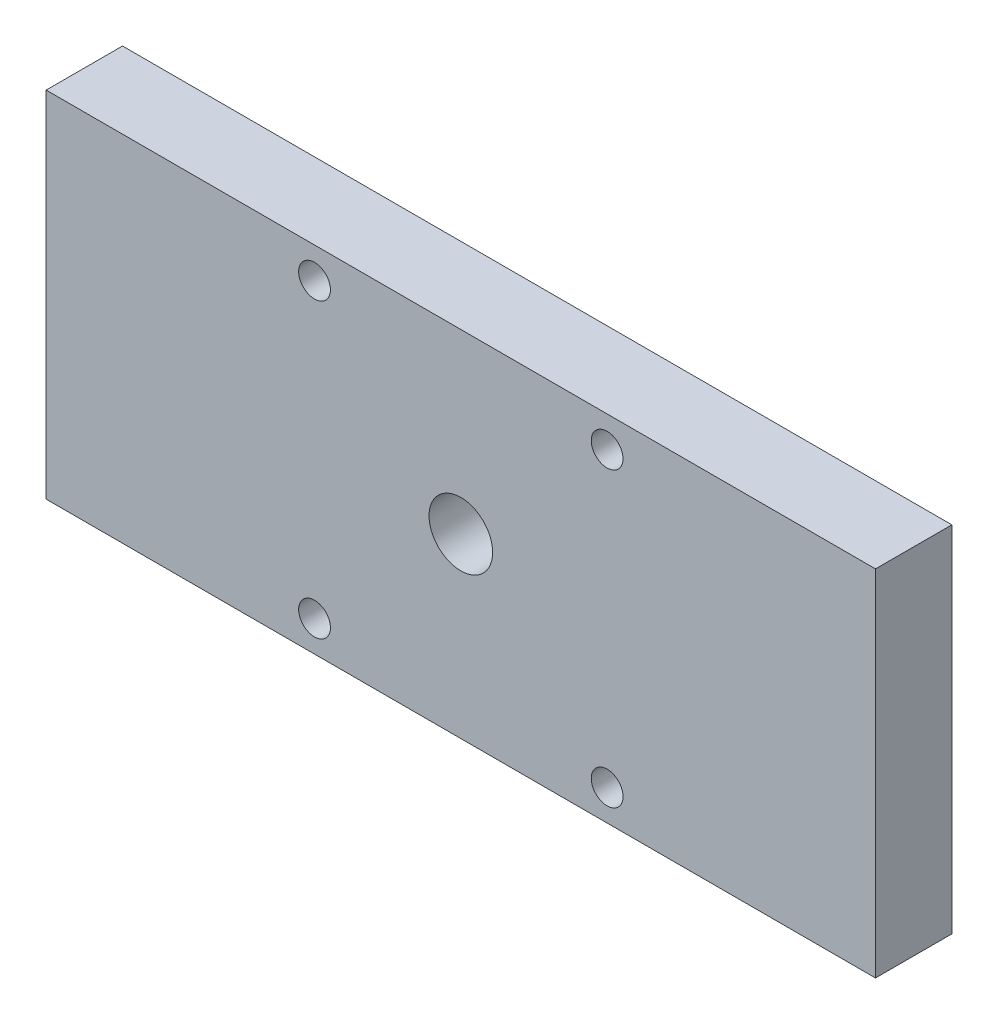
SolidWorks part; units mm, degrees
ref_plane "Plan de face" through (0, 0, 0) normal (0, 0, 1) x (1, 0, 0)
ref_plane "Plan de dessus" through (0, 0, 0) normal (0, 1, 0) x (1, 0, 0)
ref_plane "Plan de droite" through (0, 0, 0) normal (1, 0, 0) x (0, 0, -1)
sketch "Esquisse1" plane through (0, 0, 0) normal (0, 0, 1) x (1, 0, 0)
  line L1 (-22.7282, 13.3648) -> (42.4618, 13.3648)
  line L2 (-22.7282, 13.3648) -> (-22.7282, -14.4852)
  line L3 (-22.7282, -14.4852) -> (42.4618, -14.4852)
  line L4 (42.4618, 13.3648) -> (42.4618, -14.4852)
  dimension "D1" = 27.85
  dimension "D2" = 65.19
extrude "Boss.-Extru.1" add sketch "Esquisse1" along normal blind 6
sketch "Esquisse2" plane through (0, 0, 6) normal (0, 0, 1) x (1, 0, 0)
  line L0 (42.4618, 13.3648) -> (-22.7282, 13.3648) construction
  line L1 (-22.7282, 13.3648) -> (-22.7282, -14.4852) construction
  circle A0 centre (9.8668, -0.5652) radius 2.5
  circle A1 centre (-1.6332, 10.9348) radius 1.25
  circle A2 centre (21.3668, 10.9348) radius 1.25
  circle A3 centre (21.3668, -12.0652) radius 1.25
  circle A4 centre (-1.6332, -12.0652) radius 1.25
  point P12 (-22.7282, -0.5602)
  dimension "D1" = 5
  dimension "D2" = 13.93
  dimension "D3" = 2.5
  dimension "D4" = 2.5
  dimension "D5" = 2.5
  dimension "D6" = 2.5
  dimension "D7" = 11.5
  dimension "D8" = 11.5
  dimension "D9" = 11.5
  dimension "D10" = 11.5
  dimension "D11" = 11.5
  dimension "D12" = 11.5
  dimension "D13" = 11.5
  dimension "D14" = 11.5
  dimension "D15" = 32.595
extrude "Enlèv. mat.-Extru.1" cut sketch "Esquisse2" against normal blind 6
